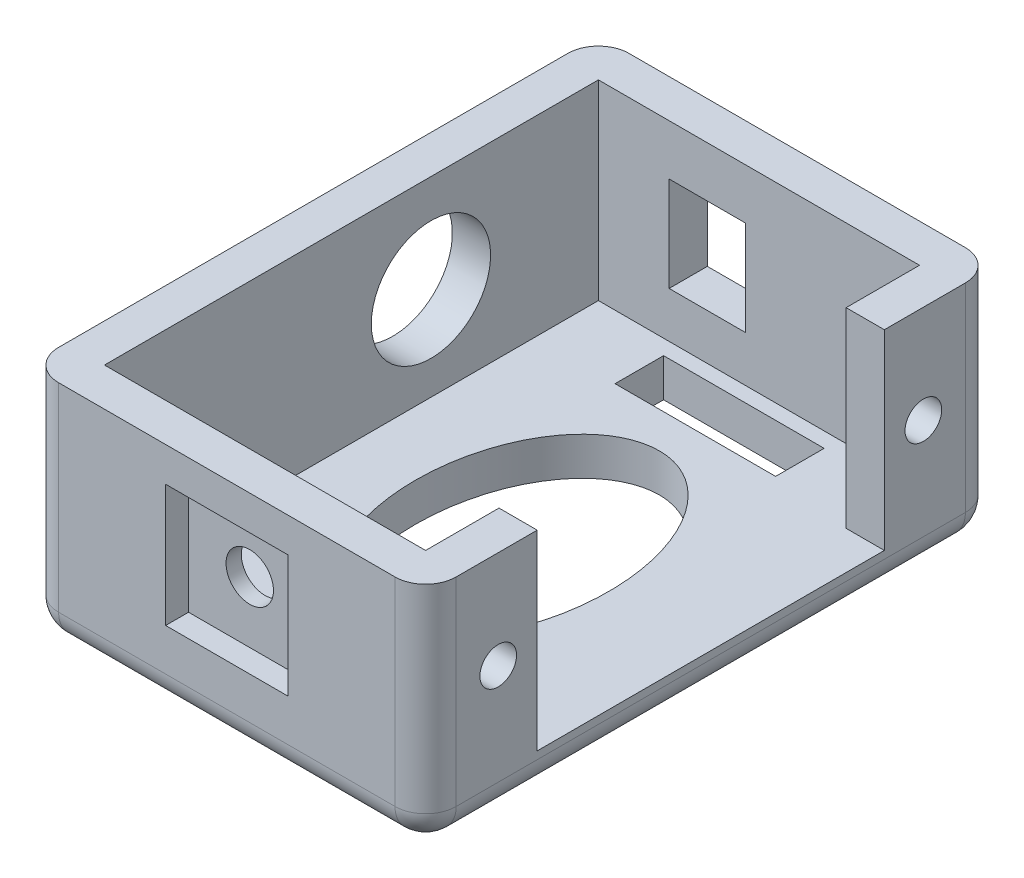
SolidWorks part; units mm, degrees
ref_plane "Front Plane" through (0, 0, 0) normal (0, 0, 1) x (1, 0, 0)
ref_plane "Top Plane" through (0, 0, 0) normal (0, 1, 0) x (1, 0, 0)
ref_plane "Right Plane" through (0, 0, 0) normal (1, 0, 0) x (0, 0, -1)
sketch "Sketch1" plane through (0, 0, 0) normal (0, 1, 0) x (1, 0, 0)
  line L1 (0, 29.9941) -> (-26, 29.9941)
  line L2 (-26, 29.9941) -> (-26, -7.3059)
  line L3 (-26, -7.3059) -> (0, -7.3059)
  line L4 (0, -7.3059) -> (0, -0.0059)
  line L5 (0, -0.0059) -> (-2.5, -0.0059)
  line L6 (-2.5, -0.0059) -> (-2.5, -4.8059)
  line L7 (-2.5, -4.8059) -> (-23.5, -4.8059)
  line L8 (-23.5, -4.8059) -> (-23.5, 27.4941)
  line L11 (0, 22.6941) -> (-2.5, 22.6941)
  line L13 (0, 29.9941) -> (0, 22.6941)
  line L14 (-23.5, 27.4941) -> (-2.5, 27.4941)
  line L15 (-2.5, 27.4941) -> (-2.5, 22.6941)
  dimension "D1" = 4.8
  dimension "D2" = 2.5
  dimension "D3" = 2.5
  dimension "D4" = 2.5
  dimension "D5" = 21
  dimension "D6" = 37.3
extrude "Boss-Extrude1" add sketch "Sketch1" along normal blind 15
sketch "Sketch2" plane through (-23.5, 0, 0) normal (1, 0, 0) x (0, 0, -1)
  line L5 (27.4941, 15) -> (27.4941, 0) construction
  line L6 (-4.8059, 0) -> (27.4941, 0)
  line L7 (-4.8059, 0) -> (-4.8059, 2.5)
  line L8 (-4.8059, 2.5) -> (27.4941, 2.5)
  line L9 (27.4941, 0) -> (27.4941, 2.5)
  dimension "D1" = 2.5
extrude "Boss-Extrude2" add sketch "Sketch2" along normal through all
sketch "Sketch3" plane through (0, 0, -29.9941) normal (0, 0, -1) x (-1, 0, 0)
  line L0 (26, 15) -> (26, 0) construction
  line L1 (13.875, 11.7) -> (18.875, 11.7)
  line L2 (13.875, 11.7) -> (13.875, 5.5)
  line L3 (13.875, 5.5) -> (18.875, 5.5)
  line L4 (18.875, 11.7) -> (18.875, 5.5)
  line L5 (0, 0) -> (26, 0) construction
  dimension "D1" = 6.2
  dimension "D2" = 5
  dimension "D3" = 7.125
  dimension "D4" = 5.5
extrude "Cut-Extrude1" cut sketch "Sketch3" against normal blind 12.5
sketch "Sketch4" plane through (-26, 0, 0) normal (-1, 0, 0) x (0, 0, 1)
  line L0 (-29.9941, 15) -> (7.3059, 15) construction
  line L1 (-29.9941, 15) -> (-29.9941, 0) construction
  circle A0 centre (-16.5441, 8.6) radius 3.9
  dimension "D1" = 7.8
  dimension "D2" = 6.4
  dimension "D3" = 13.45
extrude "Cut-Extrude2" cut sketch "Sketch4" against normal up to next
sketch "Sketch5" plane through (0, 0, 0) normal (1, 0, 0) x (0, 0, -1)
  line L0 (-0.0059, 15) -> (-0.0059, 2.5) construction
  line L1 (-7.3059, 15) -> (-0.0059, 15) construction
  circle A0 centre (-2.5559, 8.6) radius 1.2
  dimension "D2" = 2.4
  dimension "D1" = 2.55
  dimension "D3" = 6.4
extrude "Cut-Extrude3" cut sketch "Sketch5" against normal up to next (2.5 mm away)
ref_plane "Plane1" through (0, 0, -11.3441) normal (0, 0, 1) x (1, 0, 0)
mirror "Mirror1" about plane through (0, 0, -11.3441) normal (0, 0, 1) of "Cut-Extrude3"
sketch "Sketch6" plane through (0, 0, 7.3059) normal (0, 0, 1) x (1, 0, 0)
  line L0 (-2.5, 15) -> (-2.5, 2.5) construction
  line L1 (-23.5, 15) -> (-23.5, 2.5) construction
  line L2 (-2.5, 15) -> (-2.5, 2.5) construction
  line L3 (-23.5, 15) -> (-23.5, 2.5) construction
  line L4 (-23.5, 8.75) -> (-19, 8.75) construction
  line L5 (-19, 8.75) -> (-13, 8.75) construction
  line L6 (-13, 8.75) -> (-7, 8.75) construction
  line L7 (-7, 8.75) -> (-2.5, 8.75) construction
  circle A1 centre (-13, 8.75) radius 1.55
  dimension "D1" = 3.1
  dimension "D2" = 4.5
extrude "Cut-Extrude4" cut sketch "Sketch6" against normal up to next
fillet "Fillet2" radius 2 8 edges at (0, 0, -11.3441) (-13, 0, -29.9941) (-26, 0, -11.3441) (0, 7.5, -29.9941) (-26, 7.5, -29.9941) (0, 7.5, 7.3059) (-26, 7.5, 7.3059) (-13, 0, 7.3059)
sketch "Sketch7" plane through (0, 0, 7.3059) normal (0, 0, 1) x (1, 0, 0)
  line L1 (-17, 12.75) -> (-9, 12.75)
  line L2 (-17, 12.75) -> (-17, 4.75)
  line L3 (-17, 4.75) -> (-9, 4.75)
  line L4 (-9, 12.75) -> (-9, 4.75)
  circle A0 centre (-13, 8.75) radius 1.55 construction
  circle A1 centre (-13, 8.75) radius 1.55
  point P8 (-13, 12.75)
  point P10 (-9, 8.75)
  dimension "D1" = 8
extrude "Cut-Extrude5" cut sketch "Sketch7" against normal blind 1.5
sketch "Sketch8" plane through (0, 2.5, 0) normal (0, 1, 0) x (1, 0, 0)
  line L0 (-13, 1.7101) -> (-13, 11.3441) construction
  line L1 (-13, 11.3441) -> (-19.3129, 11.3441) construction
  line L2 (-13, -0.6439) -> (-13, 1.7101) construction
  line L3 (-7.75, -3.8189) -> (-18.25, -3.8189)
  line L4 (-2.5, -0.0059) -> (-13, -0.0059) construction
  line L5 (-13, -0.0059) -> (-23.5, -0.0059) construction
  line L6 (-23.5, 27.4941) -> (-23.5, -4.8059) construction
  line L7 (-7.75, -3.8189) -> (-7.75, -0.6439)
  line L8 (-7.75, -0.6439) -> (-18.25, -0.6439)
  line L9 (-18.25, -3.8189) -> (-18.25, -0.6439)
  line L10 (-7.75, 23.3321) -> (-18.25, 23.3321)
  line L11 (-7.75, 23.3321) -> (-7.75, 26.5071)
  line L12 (-7.75, 26.5071) -> (-18.25, 26.5071)
  line L13 (-18.25, 23.3321) -> (-18.25, 26.5071)
  line L14 (-13, 20.9781) -> (-13, 23.3321) construction
  line L15 (-13, 26.5071) -> (-13, 27.4941) construction
  line L16 (-2.5, 27.4941) -> (-23.5, 27.4941) construction
  line L17 (-1.375, 11.3441) -> (1.375, 11.3441) construction
  line L18 (-13, -3.8189) -> (-13, -4.8059) construction
  line L19 (-2.5, -4.8059) -> (-23.5, -4.8059) construction
  ellipse E3 centre (-13, 11.3441) end of major axis (-13, 20.9781) minor radius 6.3129
  point P15 (-13, 23.3321)
  point P16 (-13, -0.6439)
  dimension "D1" = 3.175
  dimension "D2" = 10.5
extrude "Cut-Extrude6" cut sketch "Sketch8" against normal up to next
